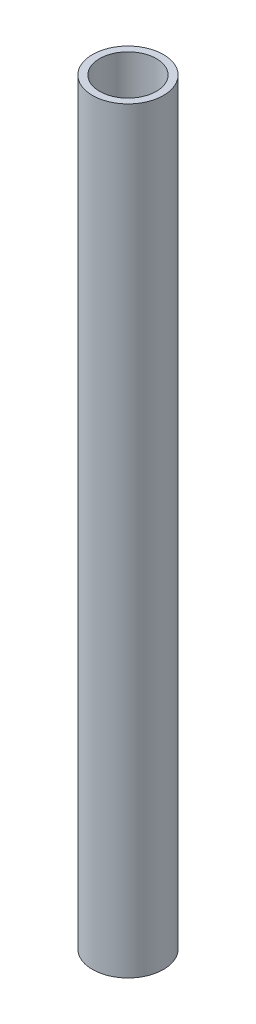
SolidWorks part; units mm, degrees
ref_plane "Front Plane" through (0, 0, 0) normal (0, 0, 1) x (1, 0, 0)
ref_plane "Top Plane" through (0, 0, 0) normal (0, 1, 0) x (1, 0, 0)
ref_plane "Right Plane" through (0, 0, 0) normal (1, 0, 0) x (0, 0, -1)
sketch "Sketch1" plane through (0, 0, 0) normal (0, 1, 0) x (1, 0, 0)
  circle A0 centre (0, 0) radius 4.7625
  circle A1 centre (0, 0) radius 3.81
  dimension "D1" = 9.525
  dimension "D2" = 7.62
extrude "Boss-Extrude1" add sketch "Sketch1" along normal blind 101.6
